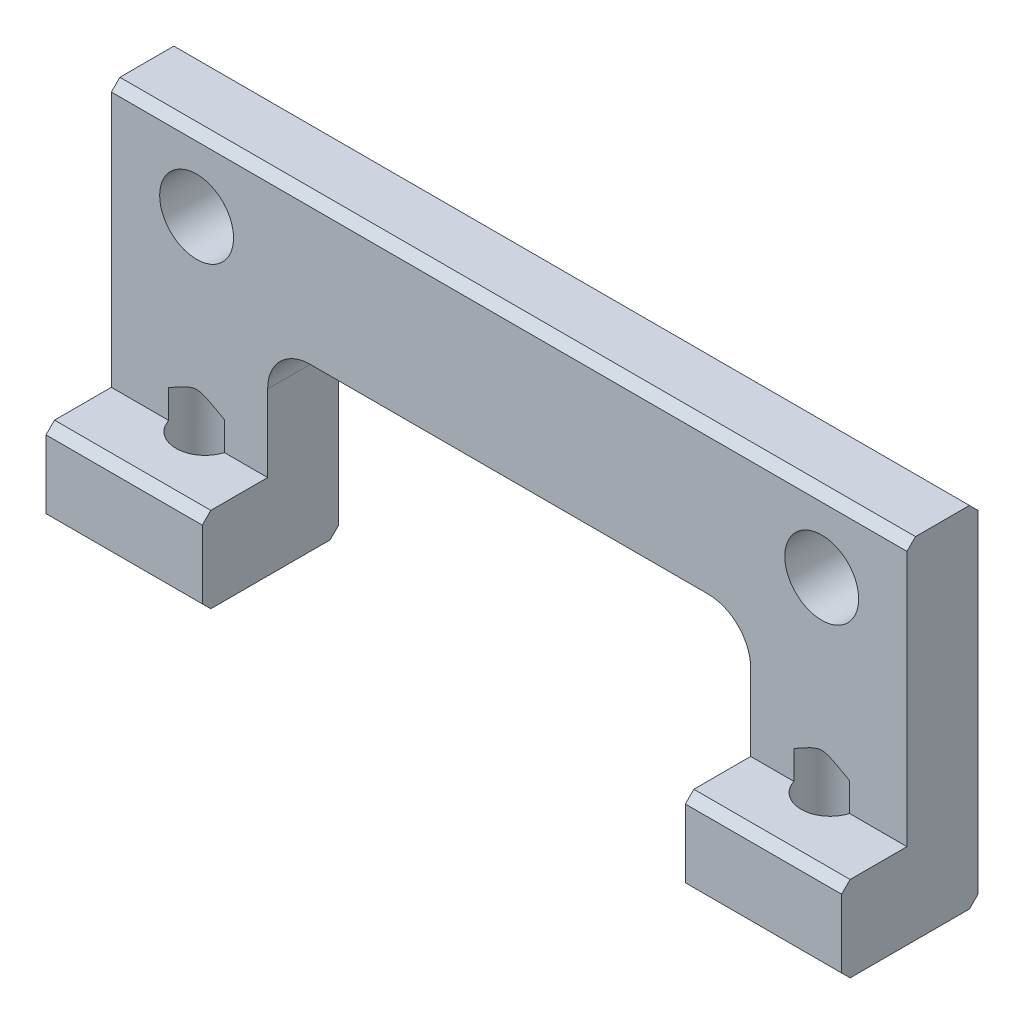
SolidWorks part; units mm, degrees
material "1060 Alloy"
ref_plane "Front Plane" through (0, 0, 0) normal (0, 0, 1) x (1, 0, 0)
ref_plane "Top Plane" through (0, 0, 0) normal (0, 1, 0) x (1, 0, 0)
ref_plane "Right Plane" through (0, 0, 0) normal (1, 0, 0) x (0, 0, -1)
ref_plane "Plane1" through (0, 0, -2.5) normal (0, 0, -1) x (-1, 0, 0)
sketch "Sketch1" plane through (0, 0, -2.5) normal (0, 0, -1) x (-1, 0, 0)
  line L0 (-8.5, 0) -> (-8.5, 12.3)
  line L1 (-8.5, 12.3) -> (-14, 12.3)
  line L2 (-14, 12.3) -> (-14, 0)
  line L3 (-14, 0) -> (-8.5, 0)
extrude "Boss-Extrude1" add sketch "Sketch1" against normal blind 4.8
sketch "Sketch2" plane through (8.5, 0, 0) normal (-1, 0, 0) x (0, 0, 1)
  line L0 (2.3, 12.3) -> (0, 12.3)
  line L1 (0, 12.3) -> (0, 3)
  line L2 (0, 3) -> (2.3, 3)
  line L3 (2.3, 3) -> (2.3, 12.3)
extrude "Cut-Extrude1" cut sketch "Sketch2" against normal through all
sketch "Sketch3" plane through (8.5, 0, 0) normal (-1, 0, 0) x (0, 0, 1)
  line L0 (0, 7.2) -> (-2.5, 7.2)
  line L1 (-2.5, 7.2) -> (-2.5, 12.3)
  line L2 (-2.5, 12.3) -> (0, 12.3)
  line L3 (0, 12.3) -> (0, 7.2)
extrude "Boss-Extrude2" add sketch "Sketch3" along normal blind 22.5
sketch "Sketch4" plane through (0, 7.2, 0) normal (0, -1, 0) x (1, 0, 0)
  line L0 (-8.5, 0) -> (-8.5, -2.5)
  line L1 (-8.5, -2.5) -> (-14, -2.5)
  line L2 (-14, -2.5) -> (-14, 0)
  line L3 (-14, 0) -> (-8.5, 0)
extrude "Boss-Extrude3" add sketch "Sketch4" along normal blind 7.2
sketch "Sketch5" plane through (0, 0, 0) normal (0, 0, 1) x (1, 0, 0)
  line L0 (-14, 0) -> (-14, 3)
  line L1 (-14, 3) -> (-8.5, 3)
  line L2 (-8.5, 3) -> (-8.5, 0)
  line L3 (-8.5, 0) -> (-14, 0)
extrude "Boss-Extrude4" add sketch "Sketch5" along normal blind 2.3
hole_wizard "#2 Clearance Hole1" positions "Sketch7" profile "Sketch6" hole size "#2" standard "ANSI Inch"
sketch "Sketch7" plane through (0, 0, -2.5) normal (0, 0, -1) x (-1, 0, 0)
  point P0 (11, 9.7)
  point P1 (-11, 9.7)
sketch "Sketch6" plane through (-11, 9.7, -2.5) normal (1, 0, 0) x (0, 1, 0)
  line L0 (0, 0) -> (0, 4.8)
  line L1 (0, 4.8) -> (1.3, 4.8)
  line L2 (1.3, 4.8) -> (1.3, 0)
  line L5 (1.3, 0) -> (0, 0)
  line L11 (0, -6.35) -> (0, 107.95) construction
  dimension "Thru Hole Dia." = 2.6
  dimension "Thru Hole Depth" = 4.8
hole_wizard "#1 Clearance Hole1" positions "Sketch9" profile "Sketch8" hole size "#1" standard "ANSI Inch"
sketch "Sketch9" plane through (0, 0, 0) normal (0, -1, 0) x (-1, 0, 0)
  point P0 (-11, 0.3)
  point P1 (11, 0.3)
sketch "Sketch8" plane through (11, 0, -0.3) normal (1, 0, 0) x (0, 0, -1)
  line L0 (0, 0) -> (0, 4.6159)
  line L1 (0, 4.6159) -> (1.025, 4)
  line L2 (1.025, 4) -> (1.025, 0)
  line L5 (1.025, 0) -> (0, 0)
  line L10 (0, 4.6159) -> (-1.025, 4) construction
  line L11 (0, -6.35) -> (0, 107.95) construction
  dimension "Hole Dia." = 2.05
  dimension "Hole Depth" = 4
  dimension "Drill Angle" = 118
chamfer "Chamfer1" distance 0.3 angle 45 11 edges at (11.25, 0, -2.5) (-11.25, 0, -2.5) (11, 0, -1.325) (0, 12.3, 0) (0, 12.3, -2.5) (-11, 0, -1.325) (9.7, 9.7, -2.5) (11.25, 0, 2.3) (-11.25, 0, 2.3) (11.25, 3, 2.3) (-11.25, 3, 2.3)
chamfer "Chamfer2" distance 0.2 angle 45 1 edges at (-12.3, 9.7, -2.5)
fillet "Fillet1" radius 1.5 2 edges at (-8.5, 7.2, -1.25) (8.5, 7.2, -1.25)
